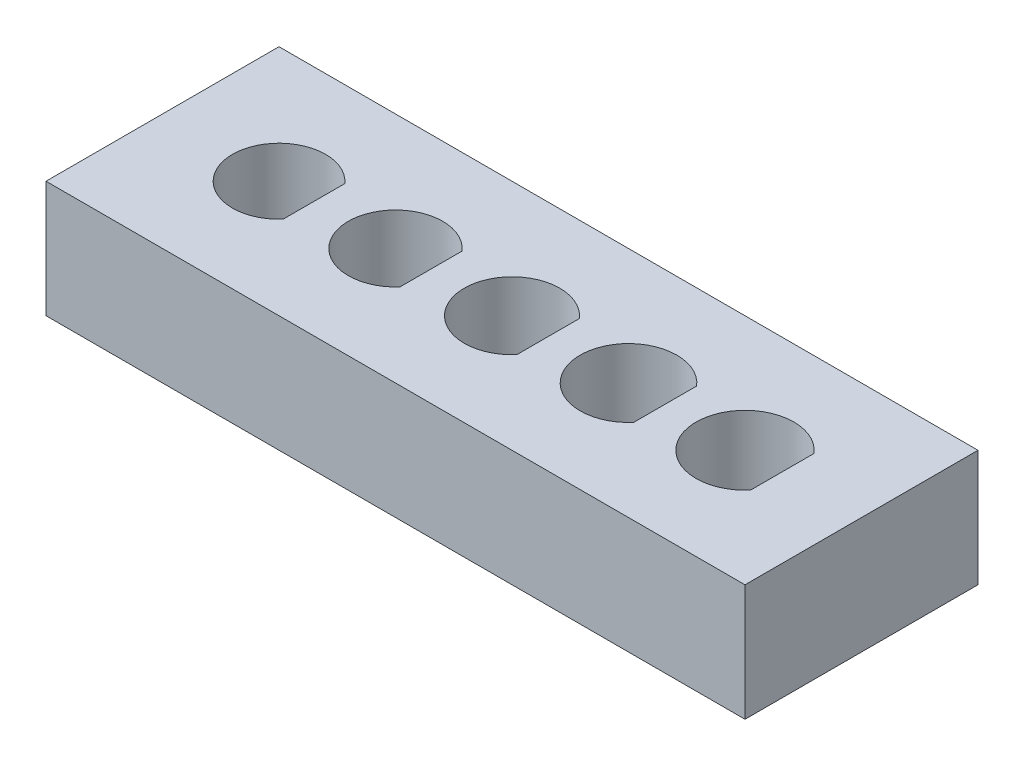
SolidWorks part; units mm, degrees
material "ABS"
ref_plane "Front Plane" through (0, 0, 0) normal (0, 0, 1) x (1, 0, 0)
ref_plane "Top Plane" through (0, 0, 0) normal (0, 1, 0) x (1, 0, 0)
ref_plane "Right Plane" through (0, 0, 0) normal (1, 0, 0) x (0, 0, -1)
sketch "Sketch1" plane through (0, 0, 0) normal (0, 1, 0) x (1, 0, 0)
  line L0 (-10, 0) -> (-15, 0) construction
  line L1 (0, -5) -> (0, 5) construction
  line L2 (-15, 5) -> (15, 5)
  line L3 (-15, 5) -> (-15, -5)
  line L4 (-15, -5) -> (15, -5)
  line L5 (15, 5) -> (15, -5)
  line L6 (-10, 0) -> (-5, 0) construction
  line L7 (-10, -2) -> (-10, 2) construction
  line L8 (-10, 0) -> (-12, 0)
  line L9 (-8.5, 1.3229) -> (-8.5, -1.3229)
  line L10 (-5, 0) -> (0, 0) construction
  line L11 (-5, -2.025) -> (-5, 2.025) construction
  line L12 (-5, 0) -> (-7.025, 0)
  line L13 (-3.475, 1.3323) -> (-3.475, -1.3323)
  line L14 (0, 0) -> (5, 0) construction
  line L15 (0, -2.05) -> (0, 2.05) construction
  line L16 (0, 0) -> (-2.05, 0)
  line L17 (1.55, 1.3416) -> (1.55, -1.3416)
  line L18 (5, 0) -> (10, 0) construction
  line L19 (5, -2.075) -> (5, 2.075) construction
  line L20 (5, 0) -> (2.925, 0)
  line L21 (6.575, 1.3509) -> (6.575, -1.3509)
  line L22 (10, 0) -> (21.9024, 0) construction
  line L23 (10, -2.1) -> (10, 2.1) construction
  line L24 (10, 0) -> (7.9, 0)
  line L25 (11.6, 1.3601) -> (11.6, -1.3601)
  arc A0 (-8.5, 1.3229) -> (-8.5, -1.3229) centre (-10, 0) ccw
  arc A1 (-3.475, 1.3323) -> (-3.475, -1.3323) centre (-5, 0) ccw
  arc A2 (1.55, 1.3416) -> (1.55, -1.3416) centre (0, 0) ccw
  arc A3 (6.575, 1.3509) -> (6.575, -1.3509) centre (5, 0) ccw
  arc A4 (11.6, 1.3601) -> (11.6, -1.3601) centre (10, 0) ccw
  dimension "D1" = 30
  dimension "D2" = 10
  dimension "D3" = 3.5
  dimension "D4" = 4
  dimension "D6" = 3.55
  dimension "D7" = 4.05
  dimension "D8" = 3.6
  dimension "D9" = 4.1
  dimension "D10" = 3.65
  dimension "D11" = 4.15
  dimension "D5" = 5
  dimension "D12" = 3.7
  dimension "D13" = 4.2
extrude "Boss-Extrude1" add sketch "Sketch1" against normal blind 5 contours L5 L2 L3 L4 A4 L25 A3 L21 A2 L17 A1 L13 A0 L9
equation "\"D5@Sketch1\"=\"D1@Sketch1\"/6"
